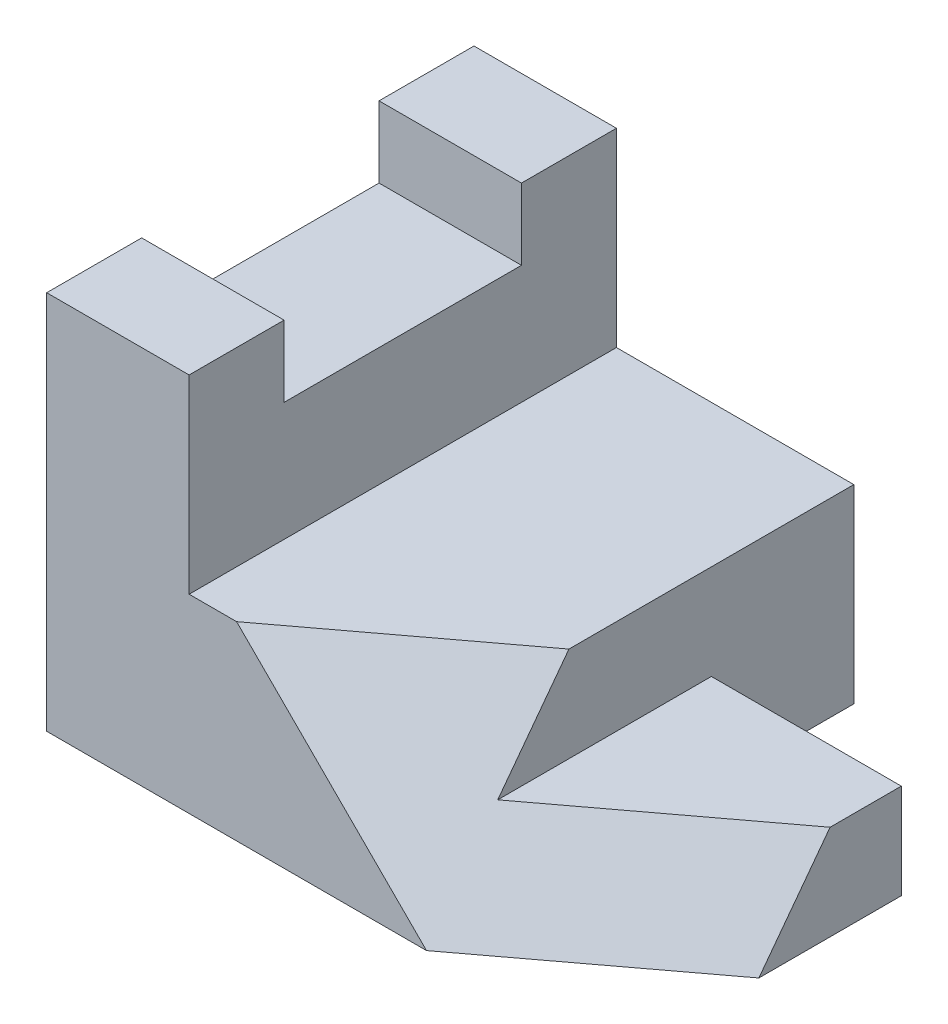
SolidWorks part; units mm, degrees
ref_plane "Front Plane" through (0, 0, 0) normal (0, 0, 1) x (1, 0, 0)
ref_plane "Top Plane" through (0, 0, 0) normal (0, 1, 0) x (1, 0, 0)
ref_plane "Right Plane" through (0, 0, 0) normal (1, 0, 0) x (0, 0, -1)
sketch "Sketch1" plane through (0, 0, 0) normal (1, 0, 0) x (0, 0, -1)
  line L1 (-57.15, 0) -> (0, 0)
  line L2 (-57.15, 0) -> (-57.15, 25.4)
  line L3 (-57.15, 25.4) -> (0, 25.4)
  line L4 (0, 0) -> (0, 25.4)
  dimension "D1" = 57.15
  dimension "D2" = 25.4
extrude "Boss-Extrude1" add sketch "Sketch1" against normal blind 57.15
sketch "Sketch2" plane through (0, 25.4, 0) normal (0, 1, 0) x (1, 0, 0)
  line L1 (0, 0) -> (-25.4, 0)
  line L2 (0, 0) -> (0, -19.05)
  line L3 (0, -19.05) -> (-25.4, -19.05)
  line L4 (-25.4, 0) -> (-25.4, -19.05)
  dimension "D1" = 19.05
  dimension "D2" = 25.4
extrude "Cut-Extrude1" cut sketch "Sketch2" against normal through all
sketch "Sketch3" plane through (0, 0, 0) normal (1, 0, 0) x (0, 0, -1)
  line L0 (-38.1, 0) -> (-19.05, 25.4) construction
  line L1 (-57.15, 0) -> (-19.05, 0) construction
  dimension "D1" = 19.05
sketch "Sketch4" plane through (0, 0, 57.15) normal (0, 0, 1) x (1, 0, 0)
  line L0 (-25.4, 0) -> (-50.8, 25.4) construction
  line L1 (-57.15, 0) -> (0, 0) construction
  line L2 (-57.15, 25.4) -> (0, 25.4) construction
  line M1 (0, 0) -> (0, 25.4)
  line M2 (0, 25.4) -> (-57.15, 25.4)
  line M4 (-57.15, 0) -> (0, 0)
  dimension "D1" = 6.35
  dimension "D2" = 31.75
sketch "Sketch7" plane through (0, 25.4, 0) normal (0, 1, 0) x (1, 0, 0)
  line L0 (-50.8, -57.15) -> (0, -19.05)
extrude "Cut-Extrude3" cut sketch "Sketch4" along direction (0.8, 0, -0.6) on the side against the normal through all contours L0 M4 M1 M2
sketch "Sketch6" plane through (-57.15, 0, 0) normal (-1, 0, 0) x (0, 0, 1)
  line L0 (0, 0) -> (0, 50.8)
  line L1 (0, 50.8) -> (12.7, 50.8)
  line L2 (12.7, 50.8) -> (12.7, 41.275)
  line L3 (0, 25.4) -> (57.15, 25.4) construction
  line L4 (12.7, 41.275) -> (44.45, 41.275)
  line L5 (28.575, 25.4) -> (28.575, 0) construction
  line L6 (57.15, 0) -> (0, 0) construction
  line L7 (0, 0) -> (57.15, 0)
  line L8 (44.45, 50.8) -> (44.45, 41.275)
  line L9 (57.15, 50.8) -> (44.45, 50.8)
  line L10 (57.15, 0) -> (57.15, 50.8)
  point P14 (28.575, 41.275)
  dimension "D1" = 28.575
  dimension "D2" = 9.525
  dimension "D3" = 50.8
  dimension "D4" = 15.875
extrude "Boss-Extrude2" add sketch "Sketch6" along normal blind 19.05
sketch "Sketch8" plane through (0, 25.4, 0) normal (0, 1, 0) x (1, 0, 0)
  line L1 (-25.4, -19.05) -> (0, -19.05)
  line L2 (-25.4, -19.05) -> (-25.4, -95.25)
  line L3 (-25.4, -95.25) -> (0, -95.25)
  line L4 (0, -19.05) -> (0, -95.25)
  dimension "D1" = 76.2
extrude "Cut-Extrude4" cut sketch "Sketch8" against normal blind 12.7
